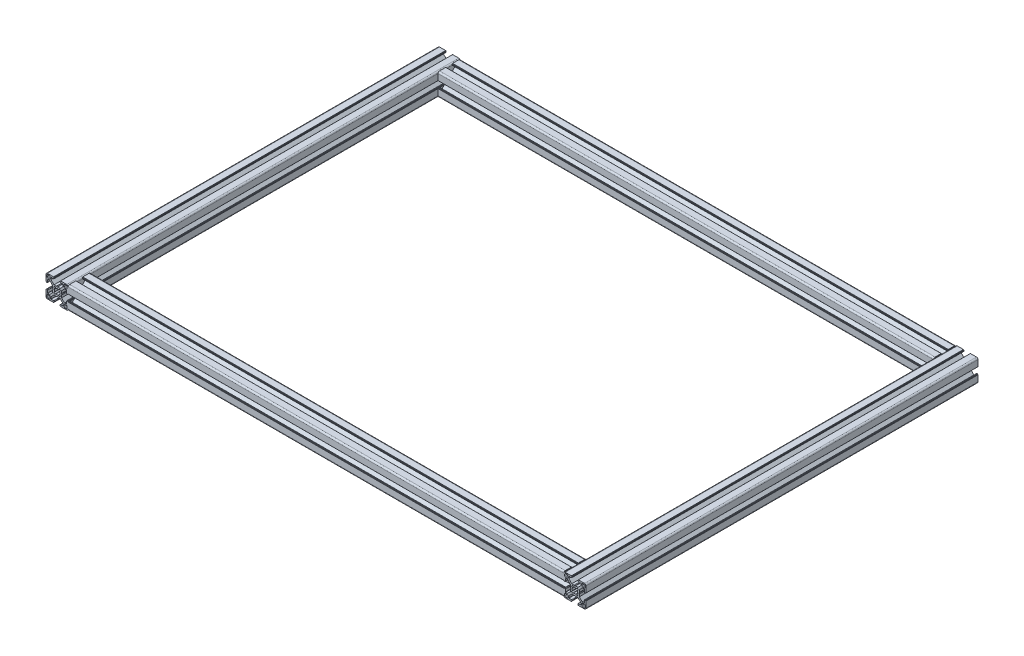
SolidWorks part; units mm, degrees
ref_plane "Front Plane" through (0, 0, 0) normal (0, 0, 1) x (1, 0, 0)
ref_plane "Top Plane" through (0, 0, 0) normal (0, 1, 0) x (1, 0, 0)
ref_plane "Right Plane" through (0, 0, 0) normal (1, 0, 0) x (0, 0, -1)
sketch "Sketch1" plane through (0, 0, 0) normal (0, 1, 0) x (1, 0, 0)
  line L1 (-350, 250) -> (350, 250)
  line L2 (-350, 250) -> (-350, -250)
  line L3 (-350, -250) -> (350, -250)
  line L4 (350, 250) -> (350, -250)
  line L5 (-350, 250) -> (350, -250) construction
  line L6 (-350, -250) -> (350, 250) construction
  point P0 (0, 0)
  dimension "D1" = 700
  dimension "D2" = 500
sketch "Sketch13" plane through (0, 0, 0) normal (0, 0, 1) x (1, 0, 0)
  line L0 (363.7, 12.7) -> (363.7, 10.5)
  line L1 (360.5, 9.5) -> (362.7, 9.5)
  line L2 (359.5, 12.7) -> (359.5, 10.5)
  line L3 (360.5, 13.7) -> (362.7, 13.7)
  line L4 (353.1359, 4.5184) -> (351.6001, 3.2806)
  line L5 (353.2806, 1.6001) -> (354.5053, 3.1547)
  line L6 (356.0045, 0.9) -> (355.4849, 0)
  line L7 (356.0045, 4.2045) -> (356.0045, 0.9)
  line L8 (350, -5.4849) -> (350.9, -6)
  line L9 (350.9, -6) -> (354.2045, -6)
  line L10 (354.2045, -6) -> (358.25, -10.05)
  line L11 (358.25, -10.05) -> (358.25, -12.6)
  line L12 (354.65, -12.8) -> (358.05, -12.8)
  line L13 (354.05, -14.3) -> (354.05, -13.4)
  line L14 (354.25, -14.5) -> (354.35, -14.5)
  line L15 (354.55, -14.8) -> (354.55, -14.7)
  line L16 (354.75, -15) -> (363, -15)
  line L17 (365, -13) -> (365, -4.75)
  line L18 (364.7, -4.55) -> (364.8, -4.55)
  line L19 (364.5, -4.35) -> (364.5, -4.25)
  line L20 (363.4, -4.05) -> (364.3, -4.05)
  line L21 (362.8, -8.05) -> (362.8, -4.65)
  line L22 (362.6, -8.25) -> (360.05, -8.25)
  line L23 (360.05, -8.25) -> (356.0045, -4.2045)
  line L24 (356.0045, -4.2045) -> (356.0045, -0.9)
  line L25 (356.0045, -0.9) -> (355.4849, 0)
  line L26 (360.05, 8.25) -> (356.0045, 4.2045)
  line L27 (362.6, 8.25) -> (360.05, 8.25)
  line L28 (362.8, 8.05) -> (362.8, 4.65)
  line L29 (363.4, 4.05) -> (364.3, 4.05)
  line L30 (364.5, 4.35) -> (364.5, 4.25)
  line L31 (364.7, 4.55) -> (364.8, 4.55)
  line L32 (365, 13) -> (365, 4.75)
  line L33 (354.75, 15) -> (363, 15)
  line L34 (354.55, 14.8) -> (354.55, 14.7)
  line L35 (354.25, 14.5) -> (354.35, 14.5)
  line L36 (354.05, 14.3) -> (354.05, 13.4)
  line L37 (354.65, 12.8) -> (358.05, 12.8)
  line L38 (358.25, 10.05) -> (358.25, 12.6)
  line L39 (354.2045, 6) -> (358.25, 10.05)
  line L40 (350.9, 6) -> (354.2045, 6)
  line L41 (350, 5.4849) -> (350.9, 6)
  line L42 (336.3, -12.7) -> (336.3, -10.5)
  line L43 (339.5, -9.5) -> (337.3, -9.5)
  line L44 (340.5, -12.7) -> (340.5, -10.5)
  line L45 (339.5, -13.7) -> (337.3, -13.7)
  line L46 (346.8641, -4.5184) -> (348.3999, -3.2806)
  line L47 (346.7194, -1.6001) -> (345.4947, -3.1547)
  line L48 (350, 5.4849) -> (349.1, 6)
  line L49 (349.1, 6) -> (345.7955, 6)
  line L50 (345.7955, 6) -> (341.75, 10.05)
  line L51 (341.75, 10.05) -> (341.75, 12.6)
  line L52 (345.35, 12.8) -> (341.95, 12.8)
  line L53 (345.95, 14.3) -> (345.95, 13.4)
  line L54 (345.75, 14.5) -> (345.65, 14.5)
  line L55 (345.45, 14.8) -> (345.45, 14.7)
  line L56 (345.25, 15) -> (337, 15)
  line L57 (335, 13) -> (335, 4.75)
  line L58 (335.3, 4.55) -> (335.2, 4.55)
  line L59 (335.5, 4.35) -> (335.5, 4.25)
  line L60 (336.6, 4.05) -> (335.7, 4.05)
  line L61 (337.2, 8.05) -> (337.2, 4.65)
  line L62 (337.4, 8.25) -> (339.95, 8.25)
  line L63 (339.95, 8.25) -> (343.9955, 4.2045)
  line L64 (343.9955, -0.9) -> (344.5151, 0)
  line L65 (343.9955, -4.2045) -> (343.9955, -0.9)
  line L66 (339.95, -8.25) -> (343.9955, -4.2045)
  line L67 (337.4, -8.25) -> (339.95, -8.25)
  line L68 (337.2, -8.05) -> (337.2, -4.65)
  line L69 (336.6, -4.05) -> (335.7, -4.05)
  line L70 (335.5, -4.35) -> (335.5, -4.25)
  line L71 (335.3, -4.55) -> (335.2, -4.55)
  line L72 (335, -13) -> (335, -4.75)
  line L73 (345.25, -15) -> (337, -15)
  line L74 (345.45, -14.8) -> (345.45, -14.7)
  line L75 (345.75, -14.5) -> (345.65, -14.5)
  line L76 (345.95, -14.3) -> (345.95, -13.4)
  line L77 (353.2806, -1.6001) -> (354.5053, -3.1547)
  line L78 (353.1359, -4.5184) -> (351.6001, -3.2806)
  line L79 (345.35, -12.8) -> (341.95, -12.8)
  line L80 (341.75, -10.05) -> (341.75, -12.6)
  line L81 (345.7955, -6) -> (341.75, -10.05)
  line L82 (349.1, -6) -> (345.7955, -6)
  line L83 (350, -5.4849) -> (349.1, -6)
  line L84 (360.5, -13.7) -> (362.7, -13.7)
  line L85 (359.5, -12.7) -> (359.5, -10.5)
  line L86 (360.5, -9.5) -> (362.7, -9.5)
  line L87 (363.7, -12.7) -> (363.7, -10.5)
  line L88 (343.9955, 4.2045) -> (343.9955, 0.9)
  line L89 (343.9955, 0.9) -> (344.5151, 0)
  line L90 (346.7194, 1.6001) -> (345.4947, 3.1547)
  line L91 (346.8641, 4.5184) -> (348.3999, 3.2806)
  line L92 (339.5, 13.7) -> (337.3, 13.7)
  line L93 (340.5, 12.7) -> (340.5, 10.5)
  line L94 (339.5, 9.5) -> (337.3, 9.5)
  line L95 (336.3, 12.7) -> (336.3, 10.5)
  line L96 (335, 0) -> (365, 0) construction
  line L97 (350, 15) -> (350, -15) construction
  line L98 (-337.4, 8.25) -> (-339.95, 8.25)
  line L99 (-354.2045, 6) -> (-358.25, 10.05)
  line L100 (-360.05, -8.25) -> (-356.0045, -4.2045)
  line L101 (-336.3, -12.7) -> (-336.3, -10.5)
  line L102 (-346.7194, 1.6001) -> (-345.4947, 3.1547)
  line L103 (-337.2, 8.05) -> (-337.2, 4.65)
  line L104 (-335.5, 4.35) -> (-335.5, 4.25)
  line L105 (-350, 5.4849) -> (-350.9, 6)
  line L106 (-362.8, 8.05) -> (-362.8, 4.65)
  line L107 (-350.9, -6) -> (-354.2045, -6)
  line L108 (-343.9955, 0.9) -> (-344.5151, 0)
  line L109 (-343.9955, 4.2045) -> (-343.9955, 0.9)
  line L110 (-339.95, -8.25) -> (-343.9955, -4.2045)
  line L111 (-345.75, 14.5) -> (-345.65, 14.5)
  line L112 (-354.05, 14.3) -> (-354.05, 13.4)
  line L113 (-350, -5.4849) -> (-350.9, -6)
  line L114 (-356.0045, 4.2045) -> (-356.0045, 0.9)
  line L115 (-336.3, 12.7) -> (-336.3, 10.5)
  line L116 (-349.1, -6) -> (-345.7955, -6)
  line L117 (-345.45, 14.8) -> (-345.45, 14.7)
  line L118 (-359.5, -12.7) -> (-359.5, -10.5)
  line L119 (-362.8, -8.05) -> (-362.8, -4.65)
  line L120 (-354.05, -14.3) -> (-354.05, -13.4)
  line L121 (-336.6, -4.05) -> (-335.7, -4.05)
  line L122 (-360.5, -9.5) -> (-362.7, -9.5)
  line L123 (-362.6, 8.25) -> (-360.05, 8.25)
  line L124 (-346.7194, -1.6001) -> (-345.4947, -3.1547)
  line L125 (-363.7, 12.7) -> (-363.7, 10.5)
  line L126 (-345.95, -14.3) -> (-345.95, -13.4)
  line L127 (-358.25, 10.05) -> (-358.25, 12.6)
  line L128 (-354.75, 15) -> (-363, 15)
  line L129 (-364.7, -4.55) -> (-364.8, -4.55)
  line L130 (-356.0045, 0.9) -> (-355.4849, 0)
  line L131 (-350, 15) -> (-350, -15) construction
  line L132 (-341.75, -10.05) -> (-341.75, -12.6)
  line L133 (-345.45, -14.8) -> (-345.45, -14.7)
  line L134 (-335.3, 4.55) -> (-335.2, 4.55)
  line L135 (-345.25, 15) -> (-337, 15)
  line L136 (-364.7, 4.55) -> (-364.8, 4.55)
  line L137 (-339.5, -13.7) -> (-337.3, -13.7)
  line L138 (-360.5, 9.5) -> (-362.7, 9.5)
  line L139 (-339.5, 9.5) -> (-337.3, 9.5)
  line L140 (-345.25, -15) -> (-337, -15)
  line L141 (-343.9955, -4.2045) -> (-343.9955, -0.9)
  line L142 (-341.75, 10.05) -> (-341.75, 12.6)
  line L143 (-354.25, 14.5) -> (-354.35, 14.5)
  line L144 (-360.05, 8.25) -> (-356.0045, 4.2045)
  line L145 (-346.8641, 4.5184) -> (-348.3999, 3.2806)
  line L146 (-345.35, -12.8) -> (-341.95, -12.8)
  line L147 (-345.95, 14.3) -> (-345.95, 13.4)
  line L148 (-360.5, -13.7) -> (-362.7, -13.7)
  line L149 (-364.5, -4.35) -> (-364.5, -4.25)
  line L150 (-346.8641, -4.5184) -> (-348.3999, -3.2806)
  line L151 (-337.4, -8.25) -> (-339.95, -8.25)
  line L152 (-353.1359, -4.5184) -> (-351.6001, -3.2806)
  line L153 (-362.6, -8.25) -> (-360.05, -8.25)
  line L154 (-354.65, -12.8) -> (-358.05, -12.8)
  line L155 (-353.1359, 4.5184) -> (-351.6001, 3.2806)
  line L156 (-345.7955, -6) -> (-341.75, -10.05)
  line L157 (-345.7955, 6) -> (-341.75, 10.05)
  line L158 (-354.65, 12.8) -> (-358.05, 12.8)
  line L159 (-354.55, 14.8) -> (-354.55, 14.7)
  line L160 (-365, -13) -> (-365, -4.75)
  line L161 (-353.2806, 1.6001) -> (-354.5053, 3.1547)
  line L162 (-365, 0) -> (-335, 0) construction
  line L163 (-345.75, -14.5) -> (-345.65, -14.5)
  line L164 (-335, -13) -> (-335, -4.75)
  line L165 (-345.35, 12.8) -> (-341.95, 12.8)
  line L166 (-364.5, 4.35) -> (-364.5, 4.25)
  line L167 (-354.75, -15) -> (-363, -15)
  line L168 (-340.5, -12.7) -> (-340.5, -10.5)
  line L169 (-335.3, -4.55) -> (-335.2, -4.55)
  line L170 (-343.9955, -0.9) -> (-344.5151, 0)
  line L171 (-350.9, 6) -> (-354.2045, 6)
  line L172 (-356.0045, -0.9) -> (-355.4849, 0)
  line L173 (-339.5, -9.5) -> (-337.3, -9.5)
  line L174 (-340.5, 12.7) -> (-340.5, 10.5)
  line L175 (-339.95, 8.25) -> (-343.9955, 4.2045)
  line L176 (-335, 13) -> (-335, 4.75)
  line L177 (-353.2806, -1.6001) -> (-354.5053, -3.1547)
  line L178 (-365, 13) -> (-365, 4.75)
  line L179 (-358.25, -10.05) -> (-358.25, -12.6)
  line L180 (-360.5, 13.7) -> (-362.7, 13.7)
  line L181 (-339.5, 13.7) -> (-337.3, 13.7)
  line L182 (-337.2, -8.05) -> (-337.2, -4.65)
  line L183 (-350, 5.4849) -> (-349.1, 6)
  line L184 (-363.4, -4.05) -> (-364.3, -4.05)
  line L185 (-354.2045, -6) -> (-358.25, -10.05)
  line L186 (-359.5, 12.7) -> (-359.5, 10.5)
  line L187 (-350, -5.4849) -> (-349.1, -6)
  line L188 (-336.6, 4.05) -> (-335.7, 4.05)
  line L189 (-349.1, 6) -> (-345.7955, 6)
  line L190 (-356.0045, -4.2045) -> (-356.0045, -0.9)
  line L191 (-354.55, -14.8) -> (-354.55, -14.7)
  line L192 (-335.5, -4.35) -> (-335.5, -4.25)
  line L193 (-363.7, -12.7) -> (-363.7, -10.5)
  line L194 (-363.4, 4.05) -> (-364.3, 4.05)
  line L195 (-354.25, -14.5) -> (-354.35, -14.5)
  arc A0 (363.7, 12.7) -> (362.7, 13.7) centre (362.7, 12.7) ccw
  arc A1 (362.7, 9.5) -> (363.7, 10.5) centre (362.7, 10.5) ccw
  arc A2 (359.5, 10.5) -> (360.5, 9.5) centre (360.5, 10.5) ccw
  arc A3 (360.5, 13.7) -> (359.5, 12.7) centre (360.5, 12.7) ccw
  arc A4 (351.6001, 3.2806) -> (348.3999, 3.2806) centre (350, 0) ccw
  arc A5 (358.25, -12.6) -> (358.05, -12.8) centre (358.05, -12.6) cw
  arc A6 (354.65, -12.8) -> (354.05, -13.4) centre (354.65, -13.4) ccw
  arc A7 (354.05, -14.3) -> (354.25, -14.5) centre (354.25, -14.3) ccw
  arc A8 (354.35, -14.5) -> (354.55, -14.7) centre (354.35, -14.7) cw
  arc A9 (354.55, -14.8) -> (354.75, -15) centre (354.75, -14.8) ccw
  arc A10 (363, -15) -> (365, -13) centre (363, -13) ccw
  arc A11 (365, -4.75) -> (364.8, -4.55) centre (364.8, -4.75) ccw
  arc A12 (364.7, -4.55) -> (364.5, -4.35) centre (364.7, -4.35) cw
  arc A13 (364.5, -4.25) -> (364.3, -4.05) centre (364.3, -4.25) ccw
  arc A14 (363.4, -4.05) -> (362.8, -4.65) centre (363.4, -4.65) ccw
  arc A15 (362.8, -8.05) -> (362.6, -8.25) centre (362.6, -8.05) cw
  arc A16 (354.5053, 3.1547) -> (353.1359, 4.5184) centre (350, 0) ccw
  arc A17 (362.8, 8.05) -> (362.6, 8.25) centre (362.6, 8.05) ccw
  arc A18 (363.4, 4.05) -> (362.8, 4.65) centre (363.4, 4.65) cw
  arc A19 (364.5, 4.25) -> (364.3, 4.05) centre (364.3, 4.25) cw
  arc A20 (364.7, 4.55) -> (364.5, 4.35) centre (364.7, 4.35) ccw
  arc A21 (365, 4.75) -> (364.8, 4.55) centre (364.8, 4.75) cw
  arc A22 (363, 15) -> (365, 13) centre (363, 13) cw
  arc A23 (354.55, 14.8) -> (354.75, 15) centre (354.75, 14.8) cw
  arc A24 (354.35, 14.5) -> (354.55, 14.7) centre (354.35, 14.7) ccw
  arc A25 (354.05, 14.3) -> (354.25, 14.5) centre (354.25, 14.3) cw
  arc A26 (354.65, 12.8) -> (354.05, 13.4) centre (354.65, 13.4) cw
  arc A27 (358.25, 12.6) -> (358.05, 12.8) centre (358.05, 12.6) ccw
  arc A28 (336.3, -12.7) -> (337.3, -13.7) centre (337.3, -12.7) ccw
  arc A29 (337.3, -9.5) -> (336.3, -10.5) centre (337.3, -10.5) ccw
  arc A30 (340.5, -10.5) -> (339.5, -9.5) centre (339.5, -10.5) ccw
  arc A31 (339.5, -13.7) -> (340.5, -12.7) centre (339.5, -12.7) ccw
  arc A32 (345.4947, -3.1547) -> (346.8641, -4.5184) centre (350, 0) ccw
  arc A33 (346.7194, 1.6001) -> (346.7194, -1.6001) centre (350, 0) ccw
  arc A34 (341.75, 12.6) -> (341.95, 12.8) centre (341.95, 12.6) cw
  arc A35 (345.35, 12.8) -> (345.95, 13.4) centre (345.35, 13.4) ccw
  arc A36 (345.95, 14.3) -> (345.75, 14.5) centre (345.75, 14.3) ccw
  arc A37 (345.65, 14.5) -> (345.45, 14.7) centre (345.65, 14.7) cw
  arc A38 (345.45, 14.8) -> (345.25, 15) centre (345.25, 14.8) ccw
  arc A39 (337, 15) -> (335, 13) centre (337, 13) ccw
  arc A40 (335, 4.75) -> (335.2, 4.55) centre (335.2, 4.75) ccw
  arc A41 (335.3, 4.55) -> (335.5, 4.35) centre (335.3, 4.35) cw
  arc A42 (335.5, 4.25) -> (335.7, 4.05) centre (335.7, 4.25) ccw
  arc A43 (336.6, 4.05) -> (337.2, 4.65) centre (336.6, 4.65) ccw
  arc A44 (337.2, 8.05) -> (337.4, 8.25) centre (337.4, 8.05) cw
  arc A45 (345.4947, 3.1547) -> (346.8641, 4.5184) centre (350, 0) cw
  arc A46 (337.2, -8.05) -> (337.4, -8.25) centre (337.4, -8.05) ccw
  arc A47 (336.6, -4.05) -> (337.2, -4.65) centre (336.6, -4.65) cw
  arc A48 (335.5, -4.25) -> (335.7, -4.05) centre (335.7, -4.25) cw
  arc A49 (353.2806, 1.6001) -> (353.2806, -1.6001) centre (350, 0) cw
  arc A50 (354.5053, -3.1547) -> (353.1359, -4.5184) centre (350, 0) cw
  arc A51 (351.6001, -3.2806) -> (348.3999, -3.2806) centre (350, 0) cw
  arc A52 (335.3, -4.55) -> (335.5, -4.35) centre (335.3, -4.35) ccw
  arc A53 (335, -4.75) -> (335.2, -4.55) centre (335.2, -4.75) cw
  arc A54 (337, -15) -> (335, -13) centre (337, -13) cw
  arc A55 (345.45, -14.8) -> (345.25, -15) centre (345.25, -14.8) cw
  arc A56 (360.5, -13.7) -> (359.5, -12.7) centre (360.5, -12.7) cw
  arc A57 (359.5, -10.5) -> (360.5, -9.5) centre (360.5, -10.5) cw
  arc A58 (362.7, -9.5) -> (363.7, -10.5) centre (362.7, -10.5) cw
  arc A59 (363.7, -12.7) -> (362.7, -13.7) centre (362.7, -12.7) cw
  arc A60 (345.65, -14.5) -> (345.45, -14.7) centre (345.65, -14.7) ccw
  arc A61 (345.95, -14.3) -> (345.75, -14.5) centre (345.75, -14.3) cw
  arc A62 (345.35, -12.8) -> (345.95, -13.4) centre (345.35, -13.4) cw
  arc A63 (341.75, -12.6) -> (341.95, -12.8) centre (341.95, -12.6) ccw
  arc A64 (339.5, 13.7) -> (340.5, 12.7) centre (339.5, 12.7) cw
  arc A65 (340.5, 10.5) -> (339.5, 9.5) centre (339.5, 10.5) cw
  arc A66 (337.3, 9.5) -> (336.3, 10.5) centre (337.3, 10.5) cw
  arc A67 (336.3, 12.7) -> (337.3, 13.7) centre (337.3, 12.7) cw
  arc A68 (-335.5, -4.25) -> (-335.7, -4.05) centre (-335.7, -4.25) ccw
  arc A69 (-335, 4.75) -> (-335.2, 4.55) centre (-335.2, 4.75) cw
  arc A70 (-360.5, -13.7) -> (-359.5, -12.7) centre (-360.5, -12.7) ccw
  arc A71 (-354.65, -12.8) -> (-354.05, -13.4) centre (-354.65, -13.4) cw
  arc A72 (-360.5, 13.7) -> (-359.5, 12.7) centre (-360.5, 12.7) cw
  arc A73 (-340.5, 10.5) -> (-339.5, 9.5) centre (-339.5, 10.5) ccw
  arc A74 (-337, 15) -> (-335, 13) centre (-337, 13) cw
  arc A75 (-345.95, 14.3) -> (-345.75, 14.5) centre (-345.75, 14.3) cw
  arc A76 (-345.35, 12.8) -> (-345.95, 13.4) centre (-345.35, 13.4) cw
  arc A77 (-339.5, -13.7) -> (-340.5, -12.7) centre (-339.5, -12.7) cw
  arc A78 (-362.7, 9.5) -> (-363.7, 10.5) centre (-362.7, 10.5) cw
  arc A79 (-345.65, -14.5) -> (-345.45, -14.7) centre (-345.65, -14.7) cw
  arc A80 (-354.5053, 3.1547) -> (-353.1359, 4.5184) centre (-350, 0) cw
  arc A81 (-363, -15) -> (-365, -13) centre (-363, -13) cw
  arc A82 (-341.75, -12.6) -> (-341.95, -12.8) centre (-341.95, -12.6) cw
  arc A83 (-345.35, -12.8) -> (-345.95, -13.4) centre (-345.35, -13.4) ccw
  arc A84 (-354.35, 14.5) -> (-354.55, 14.7) centre (-354.35, 14.7) cw
  arc A85 (-363, 15) -> (-365, 13) centre (-363, 13) ccw
  arc A86 (-358.25, -12.6) -> (-358.05, -12.8) centre (-358.05, -12.6) ccw
  arc A87 (-337.3, 9.5) -> (-336.3, 10.5) centre (-337.3, 10.5) ccw
  arc A88 (-341.75, 12.6) -> (-341.95, 12.8) centre (-341.95, 12.6) ccw
  arc A89 (-364.5, 4.25) -> (-364.3, 4.05) centre (-364.3, 4.25) ccw
  arc A90 (-359.5, 10.5) -> (-360.5, 9.5) centre (-360.5, 10.5) cw
  arc A91 (-363.4, 4.05) -> (-362.8, 4.65) centre (-363.4, 4.65) ccw
  arc A92 (-362.8, 8.05) -> (-362.6, 8.25) centre (-362.6, 8.05) cw
  arc A93 (-363.7, 12.7) -> (-362.7, 13.7) centre (-362.7, 12.7) cw
  arc A94 (-335.3, -4.55) -> (-335.5, -4.35) centre (-335.3, -4.35) cw
  arc A95 (-359.5, -10.5) -> (-360.5, -9.5) centre (-360.5, -10.5) ccw
  arc A96 (-364.7, -4.55) -> (-364.5, -4.35) centre (-364.7, -4.35) ccw
  arc A97 (-337.3, -9.5) -> (-336.3, -10.5) centre (-337.3, -10.5) cw
  arc A98 (-345.45, -14.8) -> (-345.25, -15) centre (-345.25, -14.8) ccw
  arc A99 (-337, -15) -> (-335, -13) centre (-337, -13) ccw
  arc A100 (-362.8, -8.05) -> (-362.6, -8.25) centre (-362.6, -8.05) ccw
  arc A101 (-345.4947, -3.1547) -> (-346.8641, -4.5184) centre (-350, 0) cw
  arc A102 (-337.2, -8.05) -> (-337.4, -8.25) centre (-337.4, -8.05) cw
  arc A103 (-336.6, 4.05) -> (-337.2, 4.65) centre (-336.6, 4.65) cw
  arc A104 (-345.45, 14.8) -> (-345.25, 15) centre (-345.25, 14.8) cw
  arc A105 (-363.4, -4.05) -> (-362.8, -4.65) centre (-363.4, -4.65) cw
  arc A106 (-339.5, 13.7) -> (-340.5, 12.7) centre (-339.5, 12.7) ccw
  arc A107 (-354.5053, -3.1547) -> (-353.1359, -4.5184) centre (-350, 0) ccw
  arc A108 (-364.5, -4.25) -> (-364.3, -4.05) centre (-364.3, -4.25) cw
  arc A109 (-354.35, -14.5) -> (-354.55, -14.7) centre (-354.35, -14.7) ccw
  arc A110 (-363.7, -12.7) -> (-362.7, -13.7) centre (-362.7, -12.7) ccw
  arc A111 (-346.7194, 1.6001) -> (-346.7194, -1.6001) centre (-350, 0) cw
  arc A112 (-336.3, 12.7) -> (-337.3, 13.7) centre (-337.3, 12.7) ccw
  arc A113 (-345.95, -14.3) -> (-345.75, -14.5) centre (-345.75, -14.3) ccw
  arc A114 (-358.25, 12.6) -> (-358.05, 12.8) centre (-358.05, 12.6) cw
  arc A115 (-354.55, 14.8) -> (-354.75, 15) centre (-354.75, 14.8) ccw
  arc A116 (-354.05, -14.3) -> (-354.25, -14.5) centre (-354.25, -14.3) cw
  arc A117 (-337.2, 8.05) -> (-337.4, 8.25) centre (-337.4, 8.05) ccw
  arc A118 (-335.3, 4.55) -> (-335.5, 4.35) centre (-335.3, 4.35) ccw
  arc A119 (-354.65, 12.8) -> (-354.05, 13.4) centre (-354.65, 13.4) ccw
  arc A120 (-354.55, -14.8) -> (-354.75, -15) centre (-354.75, -14.8) cw
  arc A121 (-340.5, -10.5) -> (-339.5, -9.5) centre (-339.5, -10.5) cw
  arc A122 (-335.5, 4.25) -> (-335.7, 4.05) centre (-335.7, 4.25) cw
  arc A123 (-362.7, -9.5) -> (-363.7, -10.5) centre (-362.7, -10.5) ccw
  arc A124 (-348.3999, -3.2806) -> (-351.6001, -3.2806) centre (-350, 0) cw
  arc A125 (-348.3999, 3.2806) -> (-351.6001, 3.2806) centre (-350, 0) ccw
  arc A126 (-365, 4.75) -> (-364.8, 4.55) centre (-364.8, 4.75) ccw
  arc A127 (-365, -4.75) -> (-364.8, -4.55) centre (-364.8, -4.75) cw
  arc A128 (-336.6, -4.05) -> (-337.2, -4.65) centre (-336.6, -4.65) ccw
  arc A129 (-345.65, 14.5) -> (-345.45, 14.7) centre (-345.65, 14.7) ccw
  arc A130 (-353.2806, 1.6001) -> (-353.2806, -1.6001) centre (-350, 0) ccw
  arc A131 (-335, -4.75) -> (-335.2, -4.55) centre (-335.2, -4.75) ccw
  arc A132 (-345.4947, 3.1547) -> (-346.8641, 4.5184) centre (-350, 0) ccw
  arc A133 (-354.05, 14.3) -> (-354.25, 14.5) centre (-354.25, 14.3) ccw
  arc A134 (-364.7, 4.55) -> (-364.5, 4.35) centre (-364.7, 4.35) cw
  arc A135 (-336.3, -12.7) -> (-337.3, -13.7) centre (-337.3, -12.7) cw
  point P81 (365, 15)
  point P82 (350, 15)
  point P203 (350, -15)
  point P204 (365, -15)
  point P206 (350, 0)
  point P207 (365, 0)
  point P219 (335, 0)
  point P220 (335, -15)
  point P221 (335, 15)
  point P319 (-335, 15)
  point P320 (-350, 15)
  point P441 (-350, -15)
  point P442 (-335, -15)
  point P444 (-350, 0)
  point P445 (-335, 0)
  point P457 (-365, 0)
  point P458 (-365, -15)
  point P459 (-365, 15)
extrude "Boss-Extrude1" add sketch "Sketch13" along normal mid plane 530
sketch "Sketch14" plane through (0, 0, 0) normal (1, 0, 0) x (0, 0, -1)
  line L194 (-246.8641, 4.5184) -> (-248.3999, 3.2806)
  line L195 (-235.3, 4.55) -> (-235.2, 4.55)
  line L196 (-260.5, -9.5) -> (-262.7, -9.5)
  line L197 (-258.25, 10.05) -> (-258.25, 12.6)
  line L198 (-264.5, -4.35) -> (-264.5, -4.25)
  line L199 (-259.5, 12.7) -> (-259.5, 10.5)
  line L200 (-250, -5.4849) -> (-249.1, -6)
  line L201 (-237.4, -8.25) -> (-239.95, -8.25)
  line L202 (-254.55, 14.8) -> (-254.55, 14.7)
  line L203 (-262.8, 8.05) -> (-262.8, 4.65)
  line L204 (-262.6, -8.25) -> (-260.05, -8.25)
  line L205 (-250, 15) -> (-250, -15) construction
  line L206 (-236.3, 12.7) -> (-236.3, 10.5)
  line L207 (-239.95, 8.25) -> (-243.9955, 4.2045)
  line L208 (-241.75, 10.05) -> (-241.75, 12.6)
  line L209 (-253.1359, -4.5184) -> (-251.6001, -3.2806)
  line L210 (-254.25, -14.5) -> (-254.35, -14.5)
  line L211 (-256.0045, 0.9) -> (-255.4849, 0)
  line L212 (-243.9955, -4.2045) -> (-243.9955, -0.9)
  line L213 (-245.7955, 6) -> (-241.75, 10.05)
  line L214 (-253.2806, -1.6001) -> (-254.5053, -3.1547)
  line L215 (-254.55, -14.8) -> (-254.55, -14.7)
  line L216 (-250.9, -6) -> (-254.2045, -6)
  line L217 (-245.35, -12.8) -> (-241.95, -12.8)
  line L218 (-243.9955, -0.9) -> (-244.5151, 0)
  line L219 (-249.1, 6) -> (-245.7955, 6)
  line L220 (-254.05, -14.3) -> (-254.05, -13.4)
  line L221 (-250, -5.4849) -> (-250.9, -6)
  line L222 (-265, 0) -> (-235, 0) construction
  line L223 (-243.9955, 0.9) -> (-244.5151, 0)
  line L224 (-245.75, -14.5) -> (-245.65, -14.5)
  line L225 (-235.5, -4.35) -> (-235.5, -4.25)
  line L226 (-263.7, -12.7) -> (-263.7, -10.5)
  line L227 (-250.9, 6) -> (-254.2045, 6)
  line L228 (-246.8641, -4.5184) -> (-248.3999, -3.2806)
  line L229 (-260.5, 9.5) -> (-262.7, 9.5)
  line L230 (-245.45, -14.8) -> (-245.45, -14.7)
  line L231 (-235.5, 4.35) -> (-235.5, 4.25)
  line L232 (-260.5, -13.7) -> (-262.7, -13.7)
  line L233 (-254.2045, 6) -> (-258.25, 10.05)
  line L234 (-265, -13) -> (-265, -4.75)
  line L235 (-239.95, -8.25) -> (-243.9955, -4.2045)
  line L236 (-259.5, -12.7) -> (-259.5, -10.5)
  line L237 (-262.6, 8.25) -> (-260.05, 8.25)
  line L238 (-246.7194, -1.6001) -> (-245.4947, -3.1547)
  line L239 (-253.2806, 1.6001) -> (-254.5053, 3.1547)
  line L240 (-245.95, -14.3) -> (-245.95, -13.4)
  line L241 (-237.4, 8.25) -> (-239.95, 8.25)
  line L242 (-254.65, 12.8) -> (-258.05, 12.8)
  line L243 (-264.7, 4.55) -> (-264.8, 4.55)
  line L244 (-254.65, -12.8) -> (-258.05, -12.8)
  line L245 (-239.5, -9.5) -> (-237.3, -9.5)
  line L246 (-243.9955, 4.2045) -> (-243.9955, 0.9)
  line L247 (-235, -13) -> (-235, -4.75)
  line L248 (-236.6, -4.05) -> (-235.7, -4.05)
  line L249 (-250, 5.4849) -> (-249.1, 6)
  line L250 (-239.5, -13.7) -> (-237.3, -13.7)
  line L251 (-240.5, -12.7) -> (-240.5, -10.5)
  line L252 (-245.7955, -6) -> (-241.75, -10.05)
  line L253 (-237.2, 8.05) -> (-237.2, 4.65)
  line L254 (-254.25, 14.5) -> (-254.35, 14.5)
  line L255 (-260.05, -8.25) -> (-256.0045, -4.2045)
  line L256 (-258.25, -10.05) -> (-258.25, -12.6)
  line L257 (-236.3, -12.7) -> (-236.3, -10.5)
  line L258 (-240.5, 12.7) -> (-240.5, 10.5)
  line L259 (-235, 13) -> (-235, 4.75)
  line L260 (-263.4, 4.05) -> (-264.3, 4.05)
  line L261 (-260.05, 8.25) -> (-256.0045, 4.2045)
  line L262 (-254.75, -15) -> (-263, -15)
  line L263 (-239.5, 9.5) -> (-237.3, 9.5)
  line L264 (-235.3, -4.55) -> (-235.2, -4.55)
  line L265 (-250, 5.4849) -> (-250.9, 6)
  line L266 (-256.0045, -0.9) -> (-255.4849, 0)
  line L267 (-263.4, -4.05) -> (-264.3, -4.05)
  line L268 (-253.1359, 4.5184) -> (-251.6001, 3.2806)
  line L269 (-237.2, -8.05) -> (-237.2, -4.65)
  line L270 (-254.05, 14.3) -> (-254.05, 13.4)
  line L271 (-264.5, 4.35) -> (-264.5, 4.25)
  line L272 (-260.5, 13.7) -> (-262.7, 13.7)
  line L273 (-239.5, 13.7) -> (-237.3, 13.7)
  line L274 (-249.1, -6) -> (-245.7955, -6)
  line L275 (-236.6, 4.05) -> (-235.7, 4.05)
  line L276 (-245.35, 12.8) -> (-241.95, 12.8)
  line L277 (-254.75, 15) -> (-263, 15)
  line L278 (-254.2045, -6) -> (-258.25, -10.05)
  line L279 (-256.0045, 4.2045) -> (-256.0045, 0.9)
  line L280 (-246.7194, 1.6001) -> (-245.4947, 3.1547)
  line L281 (-245.25, -15) -> (-237, -15)
  line L282 (-245.25, 15) -> (-237, 15)
  line L283 (-245.75, 14.5) -> (-245.65, 14.5)
  line L284 (-265, 13) -> (-265, 4.75)
  line L285 (-264.7, -4.55) -> (-264.8, -4.55)
  line L286 (-263.7, 12.7) -> (-263.7, 10.5)
  line L287 (-241.75, -10.05) -> (-241.75, -12.6)
  line L288 (-245.45, 14.8) -> (-245.45, 14.7)
  line L289 (-245.95, 14.3) -> (-245.95, 13.4)
  line L290 (-256.0045, -4.2045) -> (-256.0045, -0.9)
  line L291 (-262.8, -8.05) -> (-262.8, -4.65)
  line L292 (253.1359, 4.5184) -> (251.6001, 3.2806)
  line L293 (264.7, 4.55) -> (264.8, 4.55)
  line L294 (239.5, -9.5) -> (237.3, -9.5)
  line L295 (241.75, 10.05) -> (241.75, 12.6)
  line L296 (235.5, -4.35) -> (235.5, -4.25)
  line L297 (240.5, 12.7) -> (240.5, 10.5)
  line L298 (250, -5.4849) -> (250.9, -6)
  line L299 (262.6, -8.25) -> (260.05, -8.25)
  line L300 (245.45, 14.8) -> (245.45, 14.7)
  line L301 (237.2, 8.05) -> (237.2, 4.65)
  line L302 (237.4, -8.25) -> (239.95, -8.25)
  line L303 (250, 15) -> (250, -15) construction
  line L304 (263.7, 12.7) -> (263.7, 10.5)
  line L305 (260.05, 8.25) -> (256.0045, 4.2045)
  line L306 (258.25, 10.05) -> (258.25, 12.6)
  line L307 (246.8641, -4.5184) -> (248.3999, -3.2806)
  line L308 (245.75, -14.5) -> (245.65, -14.5)
  line L309 (243.9955, 0.9) -> (244.5151, 0)
  line L310 (256.0045, -4.2045) -> (256.0045, -0.9)
  line L311 (254.2045, 6) -> (258.25, 10.05)
  line L312 (246.7194, -1.6001) -> (245.4947, -3.1547)
  line L313 (245.45, -14.8) -> (245.45, -14.7)
  line L314 (249.1, -6) -> (245.7955, -6)
  line L315 (254.65, -12.8) -> (258.05, -12.8)
  line L316 (256.0045, -0.9) -> (255.4849, 0)
  line L317 (250.9, 6) -> (254.2045, 6)
  line L318 (245.95, -14.3) -> (245.95, -13.4)
  line L319 (250, -5.4849) -> (249.1, -6)
  line L320 (235, 0) -> (265, 0) construction
  line L321 (256.0045, 0.9) -> (255.4849, 0)
  line L322 (254.25, -14.5) -> (254.35, -14.5)
  line L323 (264.5, -4.35) -> (264.5, -4.25)
  line L324 (236.3, -12.7) -> (236.3, -10.5)
  line L325 (249.1, 6) -> (245.7955, 6)
  line L326 (253.1359, -4.5184) -> (251.6001, -3.2806)
  line L327 (239.5, 9.5) -> (237.3, 9.5)
  line L328 (254.55, -14.8) -> (254.55, -14.7)
  line L329 (264.5, 4.35) -> (264.5, 4.25)
  line L330 (239.5, -13.7) -> (237.3, -13.7)
  line L331 (245.7955, 6) -> (241.75, 10.05)
  line L332 (235, -13) -> (235, -4.75)
  line L333 (260.05, -8.25) -> (256.0045, -4.2045)
  line L334 (240.5, -12.7) -> (240.5, -10.5)
  line L335 (237.4, 8.25) -> (239.95, 8.25)
  line L336 (253.2806, -1.6001) -> (254.5053, -3.1547)
  line L337 (246.7194, 1.6001) -> (245.4947, 3.1547)
  line L338 (254.05, -14.3) -> (254.05, -13.4)
  line L339 (262.6, 8.25) -> (260.05, 8.25)
  line L340 (245.35, 12.8) -> (241.95, 12.8)
  line L341 (235.3, 4.55) -> (235.2, 4.55)
  line L342 (245.35, -12.8) -> (241.95, -12.8)
  line L343 (260.5, -9.5) -> (262.7, -9.5)
  line L344 (256.0045, 4.2045) -> (256.0045, 0.9)
  line L345 (265, -13) -> (265, -4.75)
  line L346 (263.4, -4.05) -> (264.3, -4.05)
  line L347 (250, 5.4849) -> (250.9, 6)
  line L348 (260.5, -13.7) -> (262.7, -13.7)
  line L349 (259.5, -12.7) -> (259.5, -10.5)
  line L350 (254.2045, -6) -> (258.25, -10.05)
  line L351 (262.8, 8.05) -> (262.8, 4.65)
  line L352 (245.75, 14.5) -> (245.65, 14.5)
  line L353 (239.95, -8.25) -> (243.9955, -4.2045)
  line L354 (241.75, -10.05) -> (241.75, -12.6)
  line L355 (263.7, -12.7) -> (263.7, -10.5)
  line L356 (259.5, 12.7) -> (259.5, 10.5)
  line L357 (265, 13) -> (265, 4.75)
  line L358 (236.6, 4.05) -> (235.7, 4.05)
  line L359 (239.95, 8.25) -> (243.9955, 4.2045)
  line L360 (245.25, -15) -> (237, -15)
  line L361 (260.5, 9.5) -> (262.7, 9.5)
  line L362 (264.7, -4.55) -> (264.8, -4.55)
  line L363 (250, 5.4849) -> (249.1, 6)
  line L364 (243.9955, -0.9) -> (244.5151, 0)
  line L365 (236.6, -4.05) -> (235.7, -4.05)
  line L366 (246.8641, 4.5184) -> (248.3999, 3.2806)
  line L367 (262.8, -8.05) -> (262.8, -4.65)
  line L368 (245.95, 14.3) -> (245.95, 13.4)
  line L369 (235.5, 4.35) -> (235.5, 4.25)
  line L370 (239.5, 13.7) -> (237.3, 13.7)
  line L371 (260.5, 13.7) -> (262.7, 13.7)
  line L372 (250.9, -6) -> (254.2045, -6)
  line L373 (263.4, 4.05) -> (264.3, 4.05)
  line L374 (254.65, 12.8) -> (258.05, 12.8)
  line L375 (245.25, 15) -> (237, 15)
  line L376 (245.7955, -6) -> (241.75, -10.05)
  line L377 (243.9955, 4.2045) -> (243.9955, 0.9)
  line L378 (253.2806, 1.6001) -> (254.5053, 3.1547)
  line L379 (254.75, -15) -> (263, -15)
  line L380 (254.75, 15) -> (263, 15)
  line L381 (254.25, 14.5) -> (254.35, 14.5)
  line L382 (235, 13) -> (235, 4.75)
  line L383 (235.3, -4.55) -> (235.2, -4.55)
  line L384 (236.3, 12.7) -> (236.3, 10.5)
  line L385 (258.25, -10.05) -> (258.25, -12.6)
  line L386 (254.55, 14.8) -> (254.55, 14.7)
  line L387 (254.05, 14.3) -> (254.05, 13.4)
  line L388 (243.9955, -4.2045) -> (243.9955, -0.9)
  line L389 (237.2, -8.05) -> (237.2, -4.65)
  arc A136 (-236.6, 4.05) -> (-237.2, 4.65) centre (-236.6, 4.65) cw
  arc A137 (-245.35, 12.8) -> (-245.95, 13.4) centre (-245.35, 13.4) cw
  arc A138 (-254.5053, -3.1547) -> (-253.1359, -4.5184) centre (-250, 0) ccw
  arc A139 (-254.65, -12.8) -> (-254.05, -13.4) centre (-254.65, -13.4) cw
  arc A140 (-237.3, 9.5) -> (-236.3, 10.5) centre (-237.3, 10.5) ccw
  arc A141 (-245.35, -12.8) -> (-245.95, -13.4) centre (-245.35, -13.4) ccw
  arc A142 (-263.4, 4.05) -> (-262.8, 4.65) centre (-263.4, 4.65) ccw
  arc A143 (-263.4, -4.05) -> (-262.8, -4.65) centre (-263.4, -4.65) cw
  arc A144 (-263.7, -12.7) -> (-262.7, -13.7) centre (-262.7, -12.7) ccw
  arc A145 (-264.7, -4.55) -> (-264.5, -4.35) centre (-264.7, -4.35) ccw
  arc A146 (-259.5, 10.5) -> (-260.5, 9.5) centre (-260.5, 10.5) cw
  arc A147 (-235.3, -4.55) -> (-235.5, -4.35) centre (-235.3, -4.35) cw
  arc A148 (-237, 15) -> (-235, 13) centre (-237, 13) cw
  arc A149 (-263, 15) -> (-265, 13) centre (-263, 13) ccw
  arc A150 (-263.7, 12.7) -> (-262.7, 13.7) centre (-262.7, 12.7) cw
  arc A151 (-237.2, 8.05) -> (-237.4, 8.25) centre (-237.4, 8.05) ccw
  arc A152 (-235.5, 4.25) -> (-235.7, 4.05) centre (-235.7, 4.25) cw
  arc A153 (-246.7194, 1.6001) -> (-246.7194, -1.6001) centre (-250, 0) cw
  arc A154 (-254.05, -14.3) -> (-254.25, -14.5) centre (-254.25, -14.3) cw
  arc A155 (-245.65, -14.5) -> (-245.45, -14.7) centre (-245.65, -14.7) cw
  arc A156 (-258.25, 12.6) -> (-258.05, 12.8) centre (-258.05, 12.6) cw
  arc A157 (-254.65, 12.8) -> (-254.05, 13.4) centre (-254.65, 13.4) ccw
  arc A158 (-239.5, -13.7) -> (-240.5, -12.7) centre (-239.5, -12.7) cw
  arc A159 (-262.7, 9.5) -> (-263.7, 10.5) centre (-262.7, 10.5) cw
  arc A160 (-240.5, 10.5) -> (-239.5, 9.5) centre (-239.5, 10.5) ccw
  arc A161 (-237.2, -8.05) -> (-237.4, -8.25) centre (-237.4, -8.05) cw
  arc A162 (-262.7, -9.5) -> (-263.7, -10.5) centre (-262.7, -10.5) ccw
  arc A163 (-254.5053, 3.1547) -> (-253.1359, 4.5184) centre (-250, 0) cw
  arc A164 (-239.5, 13.7) -> (-240.5, 12.7) centre (-239.5, 12.7) ccw
  arc A165 (-245.65, 14.5) -> (-245.45, 14.7) centre (-245.65, 14.7) ccw
  arc A166 (-254.35, 14.5) -> (-254.55, 14.7) centre (-254.35, 14.7) cw
  arc A167 (-254.55, -14.8) -> (-254.75, -15) centre (-254.75, -14.8) cw
  arc A168 (-248.3999, 3.2806) -> (-251.6001, 3.2806) centre (-250, 0) ccw
  arc A169 (-260.5, -13.7) -> (-259.5, -12.7) centre (-260.5, -12.7) ccw
  arc A170 (-264.5, 4.25) -> (-264.3, 4.05) centre (-264.3, 4.25) ccw
  arc A171 (-237.3, -9.5) -> (-236.3, -10.5) centre (-237.3, -10.5) cw
  arc A172 (-235.3, 4.55) -> (-235.5, 4.35) centre (-235.3, 4.35) ccw
  arc A173 (-245.4947, -3.1547) -> (-246.8641, -4.5184) centre (-250, 0) cw
  arc A174 (-260.5, 13.7) -> (-259.5, 12.7) centre (-260.5, 12.7) cw
  arc A175 (-245.45, -14.8) -> (-245.25, -15) centre (-245.25, -14.8) ccw
  arc A176 (-235, 4.75) -> (-235.2, 4.55) centre (-235.2, 4.75) cw
  arc A177 (-253.2806, 1.6001) -> (-253.2806, -1.6001) centre (-250, 0) ccw
  arc A178 (-265, -4.75) -> (-264.8, -4.55) centre (-264.8, -4.75) cw
  arc A179 (-236.3, -12.7) -> (-237.3, -13.7) centre (-237.3, -12.7) cw
  arc A180 (-237, -15) -> (-235, -13) centre (-237, -13) ccw
  arc A181 (-262.8, 8.05) -> (-262.6, 8.25) centre (-262.6, 8.05) cw
  arc A182 (-262.8, -8.05) -> (-262.6, -8.25) centre (-262.6, -8.05) ccw
  arc A183 (-245.95, 14.3) -> (-245.75, 14.5) centre (-245.75, 14.3) cw
  arc A184 (-259.5, -10.5) -> (-260.5, -9.5) centre (-260.5, -10.5) ccw
  arc A185 (-240.5, -10.5) -> (-239.5, -9.5) centre (-239.5, -10.5) cw
  arc A186 (-236.3, 12.7) -> (-237.3, 13.7) centre (-237.3, 12.7) ccw
  arc A187 (-241.75, -12.6) -> (-241.95, -12.8) centre (-241.95, -12.6) cw
  arc A188 (-236.6, -4.05) -> (-237.2, -4.65) centre (-236.6, -4.65) ccw
  arc A189 (-241.75, 12.6) -> (-241.95, 12.8) centre (-241.95, 12.6) ccw
  arc A190 (-265, 4.75) -> (-264.8, 4.55) centre (-264.8, 4.75) ccw
  arc A191 (-245.95, -14.3) -> (-245.75, -14.5) centre (-245.75, -14.3) ccw
  arc A192 (-245.45, 14.8) -> (-245.25, 15) centre (-245.25, 14.8) cw
  arc A193 (-254.05, 14.3) -> (-254.25, 14.5) centre (-254.25, 14.3) ccw
  arc A194 (-258.25, -12.6) -> (-258.05, -12.8) centre (-258.05, -12.6) ccw
  arc A195 (-235, -4.75) -> (-235.2, -4.55) centre (-235.2, -4.75) ccw
  arc A196 (-254.55, 14.8) -> (-254.75, 15) centre (-254.75, 14.8) ccw
  arc A197 (-264.7, 4.55) -> (-264.5, 4.35) centre (-264.7, 4.35) cw
  arc A198 (-263, -15) -> (-265, -13) centre (-263, -13) cw
  arc A199 (-235.5, -4.25) -> (-235.7, -4.05) centre (-235.7, -4.25) ccw
  arc A200 (-245.4947, 3.1547) -> (-246.8641, 4.5184) centre (-250, 0) ccw
  arc A201 (-264.5, -4.25) -> (-264.3, -4.05) centre (-264.3, -4.25) cw
  arc A202 (-248.3999, -3.2806) -> (-251.6001, -3.2806) centre (-250, 0) cw
  arc A203 (-254.35, -14.5) -> (-254.55, -14.7) centre (-254.35, -14.7) ccw
  arc A204 (263.4, 4.05) -> (262.8, 4.65) centre (263.4, 4.65) cw
  arc A205 (254.65, 12.8) -> (254.05, 13.4) centre (254.65, 13.4) cw
  arc A206 (245.4947, -3.1547) -> (246.8641, -4.5184) centre (250, 0) ccw
  arc A207 (245.35, -12.8) -> (245.95, -13.4) centre (245.35, -13.4) cw
  arc A208 (262.7, 9.5) -> (263.7, 10.5) centre (262.7, 10.5) ccw
  arc A209 (254.65, -12.8) -> (254.05, -13.4) centre (254.65, -13.4) ccw
  arc A210 (236.6, 4.05) -> (237.2, 4.65) centre (236.6, 4.65) ccw
  arc A211 (236.6, -4.05) -> (237.2, -4.65) centre (236.6, -4.65) cw
  arc A212 (236.3, -12.7) -> (237.3, -13.7) centre (237.3, -12.7) ccw
  arc A213 (235.3, -4.55) -> (235.5, -4.35) centre (235.3, -4.35) ccw
  arc A214 (240.5, 10.5) -> (239.5, 9.5) centre (239.5, 10.5) cw
  arc A215 (264.7, -4.55) -> (264.5, -4.35) centre (264.7, -4.35) cw
  arc A216 (263, 15) -> (265, 13) centre (263, 13) cw
  arc A217 (237, 15) -> (235, 13) centre (237, 13) ccw
  arc A218 (236.3, 12.7) -> (237.3, 13.7) centre (237.3, 12.7) cw
  arc A219 (262.8, 8.05) -> (262.6, 8.25) centre (262.6, 8.05) ccw
  arc A220 (264.5, 4.25) -> (264.3, 4.05) centre (264.3, 4.25) cw
  arc A221 (253.2806, 1.6001) -> (253.2806, -1.6001) centre (250, 0) cw
  arc A222 (245.95, -14.3) -> (245.75, -14.5) centre (245.75, -14.3) cw
  arc A223 (254.35, -14.5) -> (254.55, -14.7) centre (254.35, -14.7) cw
  arc A224 (241.75, 12.6) -> (241.95, 12.8) centre (241.95, 12.6) cw
  arc A225 (245.35, 12.8) -> (245.95, 13.4) centre (245.35, 13.4) ccw
  arc A226 (260.5, -13.7) -> (259.5, -12.7) centre (260.5, -12.7) cw
  arc A227 (237.3, 9.5) -> (236.3, 10.5) centre (237.3, 10.5) cw
  arc A228 (259.5, 10.5) -> (260.5, 9.5) centre (260.5, 10.5) ccw
  arc A229 (262.8, -8.05) -> (262.6, -8.25) centre (262.6, -8.05) cw
  arc A230 (237.3, -9.5) -> (236.3, -10.5) centre (237.3, -10.5) ccw
  arc A231 (245.4947, 3.1547) -> (246.8641, 4.5184) centre (250, 0) cw
  arc A232 (260.5, 13.7) -> (259.5, 12.7) centre (260.5, 12.7) ccw
  arc A233 (254.35, 14.5) -> (254.55, 14.7) centre (254.35, 14.7) ccw
  arc A234 (245.65, 14.5) -> (245.45, 14.7) centre (245.65, 14.7) cw
  arc A235 (245.45, -14.8) -> (245.25, -15) centre (245.25, -14.8) cw
  arc A236 (251.6001, 3.2806) -> (248.3999, 3.2806) centre (250, 0) ccw
  arc A237 (239.5, -13.7) -> (240.5, -12.7) centre (239.5, -12.7) ccw
  arc A238 (235.5, 4.25) -> (235.7, 4.05) centre (235.7, 4.25) ccw
  arc A239 (262.7, -9.5) -> (263.7, -10.5) centre (262.7, -10.5) cw
  arc A240 (264.7, 4.55) -> (264.5, 4.35) centre (264.7, 4.35) ccw
  arc A241 (254.5053, -3.1547) -> (253.1359, -4.5184) centre (250, 0) cw
  arc A242 (239.5, 13.7) -> (240.5, 12.7) centre (239.5, 12.7) cw
  arc A243 (254.55, -14.8) -> (254.75, -15) centre (254.75, -14.8) ccw
  arc A244 (265, 4.75) -> (264.8, 4.55) centre (264.8, 4.75) cw
  arc A245 (246.7194, 1.6001) -> (246.7194, -1.6001) centre (250, 0) ccw
  arc A246 (235, -4.75) -> (235.2, -4.55) centre (235.2, -4.75) cw
  arc A247 (263.7, -12.7) -> (262.7, -13.7) centre (262.7, -12.7) cw
  arc A248 (263, -15) -> (265, -13) centre (263, -13) ccw
  arc A249 (237.2, 8.05) -> (237.4, 8.25) centre (237.4, 8.05) cw
  arc A250 (237.2, -8.05) -> (237.4, -8.25) centre (237.4, -8.05) ccw
  arc A251 (254.05, 14.3) -> (254.25, 14.5) centre (254.25, 14.3) cw
  arc A252 (240.5, -10.5) -> (239.5, -9.5) centre (239.5, -10.5) ccw
  arc A253 (259.5, -10.5) -> (260.5, -9.5) centre (260.5, -10.5) cw
  arc A254 (263.7, 12.7) -> (262.7, 13.7) centre (262.7, 12.7) ccw
  arc A255 (258.25, -12.6) -> (258.05, -12.8) centre (258.05, -12.6) cw
  arc A256 (263.4, -4.05) -> (262.8, -4.65) centre (263.4, -4.65) ccw
  arc A257 (258.25, 12.6) -> (258.05, 12.8) centre (258.05, 12.6) ccw
  arc A258 (235, 4.75) -> (235.2, 4.55) centre (235.2, 4.75) ccw
  arc A259 (254.05, -14.3) -> (254.25, -14.5) centre (254.25, -14.3) ccw
  arc A260 (254.55, 14.8) -> (254.75, 15) centre (254.75, 14.8) cw
  arc A261 (245.95, 14.3) -> (245.75, 14.5) centre (245.75, 14.3) ccw
  arc A262 (241.75, -12.6) -> (241.95, -12.8) centre (241.95, -12.6) ccw
  arc A263 (265, -4.75) -> (264.8, -4.55) centre (264.8, -4.75) ccw
  arc A264 (245.45, 14.8) -> (245.25, 15) centre (245.25, 14.8) ccw
  arc A265 (235.3, 4.55) -> (235.5, 4.35) centre (235.3, 4.35) cw
  arc A266 (237, -15) -> (235, -13) centre (237, -13) cw
  arc A267 (264.5, -4.25) -> (264.3, -4.05) centre (264.3, -4.25) ccw
  arc A268 (254.5053, 3.1547) -> (253.1359, 4.5184) centre (250, 0) ccw
  arc A269 (235.5, -4.25) -> (235.7, -4.05) centre (235.7, -4.25) cw
  arc A270 (251.6001, -3.2806) -> (248.3999, -3.2806) centre (250, 0) cw
  arc A271 (245.65, -14.5) -> (245.45, -14.7) centre (245.65, -14.7) ccw
  point P319 (-235, 15)
  point P320 (-250, 15)
  point P441 (-250, -15)
  point P442 (-235, -15)
  point P444 (-250, 0)
  point P445 (-235, 0)
  point P457 (-265, 0)
  point P458 (-265, -15)
  point P459 (-265, 15)
  point P557 (265, 15)
  point P558 (250, 15)
  point P679 (250, -15)
  point P680 (265, -15)
  point P682 (250, 0)
  point P683 (265, 0)
  point P695 (235, 0)
  point P696 (235, -15)
  point P697 (235, 15)
extrude "Boss-Extrude2" add sketch "Sketch14" along normal mid plane 670
